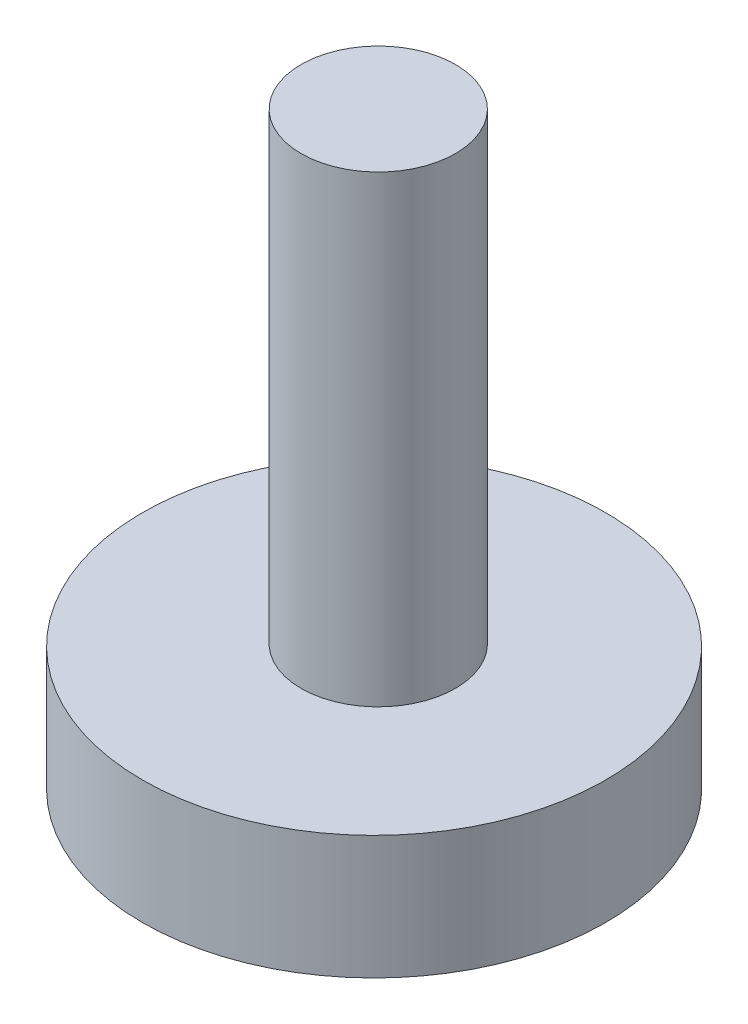
SolidWorks part; units mm, degrees
ref_plane "Спереди" through (0, 0, 0) normal (0, 0, 1) x (1, 0, 0)
ref_plane "Сверху" through (0, 0, 0) normal (0, 1, 0) x (1, 0, 0)
ref_plane "Справа" through (0, 0, 0) normal (1, 0, 0) x (0, 0, -1)
sketch "Эскиз1" plane through (0, 0, 0) normal (0, 1, 0) x (1, 0, 0)
  circle A0 centre (0, 0) radius 7.5
  dimension "D1" = 15
extrude "Бобышка-Вытянуть1" add sketch "Эскиз1" along normal blind 4
sketch "Эскиз2" plane through (0, 4, 0) normal (0, 1, 0) x (1, 0, 0)
  circle A0 centre (0, 0.1363) radius 2.5
  dimension "D1" = 5
extrude "Бобышка-Вытянуть2" add sketch "Эскиз2" along normal blind 15
